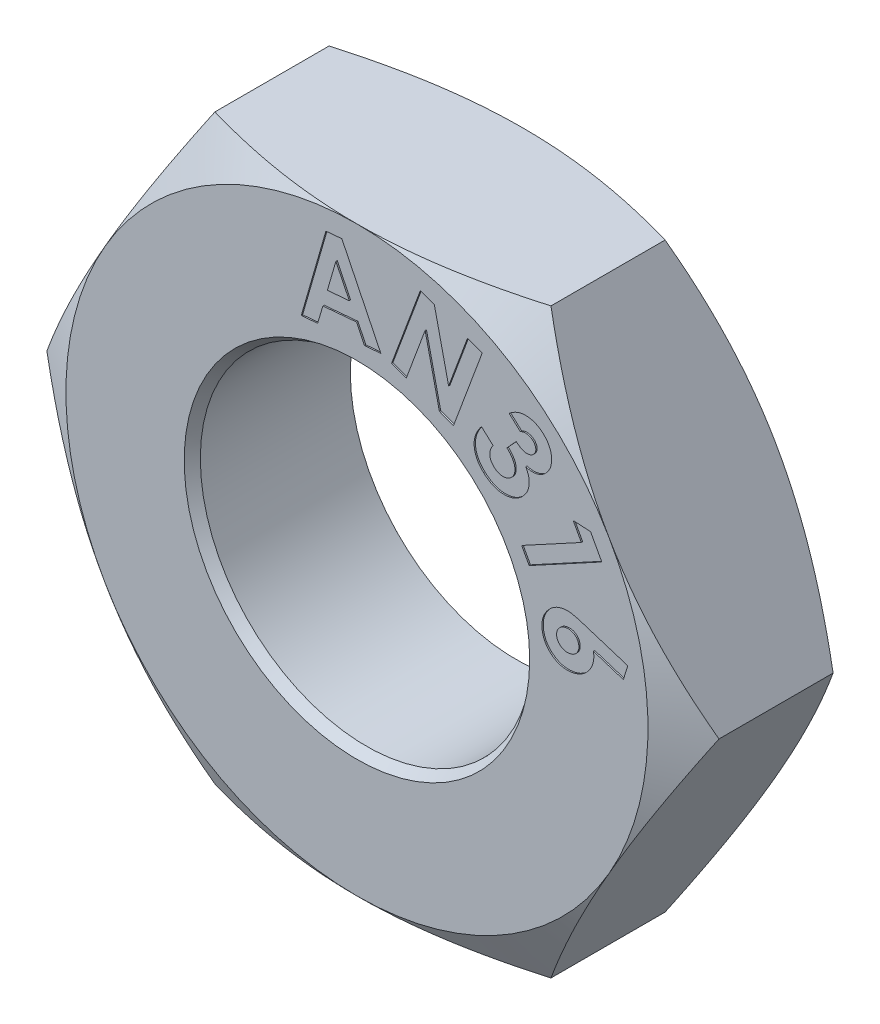
SolidWorks part; units mm, degrees
material "AISI 4130 Steel, normalized at 870C"
ref_plane "Front Plane" through (0, 0, 0) normal (0, 0, 1) x (1, 0, 0)
ref_plane "Top Plane" through (0, 0, 0) normal (0, 1, 0) x (1, 0, 0)
ref_plane "Right Plane" through (0, 0, 0) normal (1, 0, 0) x (0, 0, -1)
sketch "Sketch2" plane through (0, 0, 0) normal (0, 0, 1) x (1, 0, 0)
  line L1 (3.2116, -5.5626) -> (6.4231, 0)
  line L2 (6.4231, 0) -> (3.2116, 5.5626)
  line L3 (3.2116, 5.5626) -> (-3.2116, 5.5626)
  line L4 (-3.2116, 5.5626) -> (-6.4231, 0)
  line L5 (-6.4231, 0) -> (-3.2116, -5.5626)
  line L6 (-3.2116, -5.5626) -> (3.2116, -5.5626)
  circle A0 centre (0, 0) radius 5.5626 construction
  circle A1 centre (0, 0) radius 3.175
  dimension "Diameter A" = 11.1252
  dimension "Thread T" = 6.35
extrude "Nut" add sketch "Sketch2" along normal blind 3.175
sketch "Sketch3" plane through (0, 0, 3.175) normal (0, 0, 1) x (1, 0, 0)
  line L0 (3.2116, -5.5626) -> (6.4231, 0) construction
  circle A0 centre (0, 0) radius 5.5626
extrude "Cut-Extrude1" cut sketch "Sketch3" against normal blind 3.175 draft 60 flip side to cut
sketch "Sketch4" plane through (0, 0, 0) normal (0, 0, -1) x (-1, 0, 0)
  line L0 (-6.4231, 0) -> (-3.2116, 5.5626) construction
  circle A0 centre (0, 0) radius 5.5626
extrude "Cut-Extrude2" cut sketch "Sketch4" against normal blind 3.175 draft 60 flip side to cut
chamfer "Chamfer1" distance 0.127 angle 55 2 edges at (3.175, 0, 3.175) (3.175, 0, 0)
sketch "Sketch5" plane through (0, 0, 3.175) normal (0, 0, 1) x (1, 0, 0)
  circle A0 centre (0, 0) radius 3.683 construction
  circle A1 centre (0, 0) radius 3.302 construction
  text T0 "AN316" font "Century Gothic" height in points 6
  dimension "D1" = 0.381
extrude "Cut-Extrude3" cut sketch "Sketch5" against normal blind 0.0254
